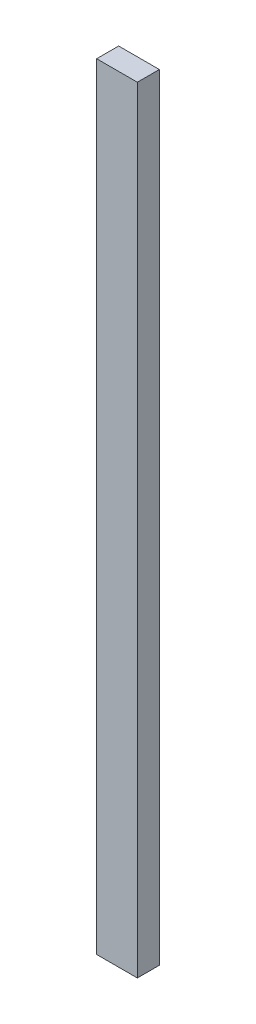
SolidWorks part; units mm, degrees
ref_plane "Plano frontal" through (0, 0, 0) normal (0, 0, 1) x (1, 0, 0)
ref_plane "Plano superior" through (0, 0, 0) normal (0, 1, 0) x (1, 0, 0)
ref_plane "Plano direito" through (0, 0, 0) normal (1, 0, 0) x (0, 0, -1)
sketch "Sketch1" plane through (0, 0, 0) normal (0, 1, 0) x (1, 0, 0)
  line L1 (-41.4227, 17.1818) -> (63.5326, 17.1818)
  line L2 (-41.4227, 17.1818) -> (-41.4227, -39.558)
  line L3 (-41.4227, -39.558) -> (63.5326, -39.558)
  line L4 (63.5326, 17.1818) -> (63.5326, -39.558)
extrude "Boss-Extrude1" add sketch "Sketch1" along normal blind 2000
